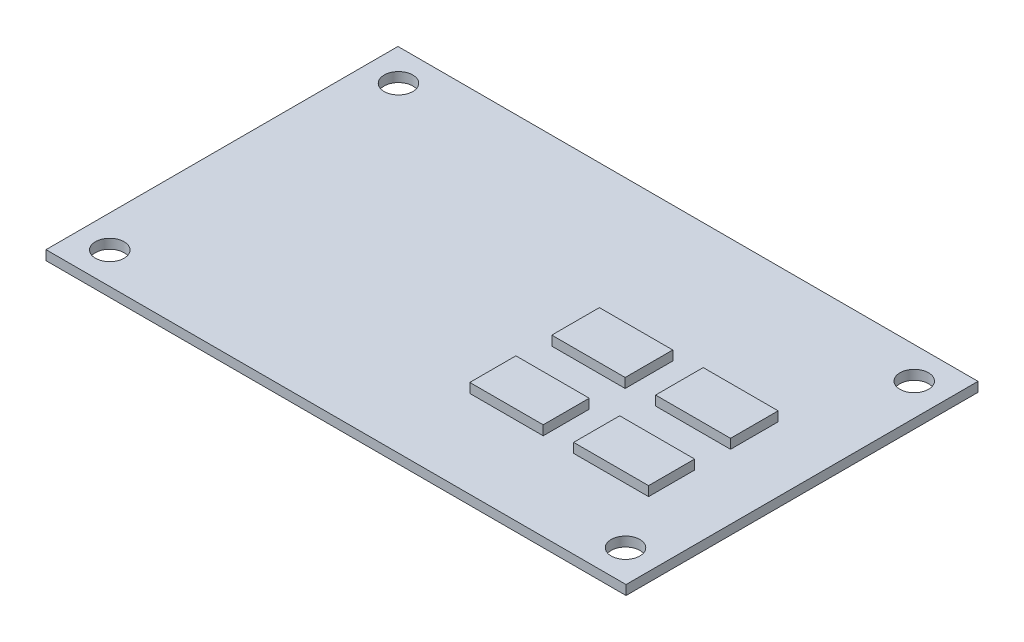
SolidWorks part; units mm, degrees
ref_plane "前视基准面" through (0, 0, 0) normal (0, 0, 1) x (1, 0, 0)
ref_plane "上视基准面" through (0, 0, 0) normal (0, 1, 0) x (1, 0, 0)
ref_plane "右视基准面" through (0, 0, 0) normal (1, 0, 0) x (0, 0, -1)
sketch "草图2" plane through (0, 0, 0) normal (0, 1, 0) x (1, 0, 0)
  line L1 (-30.365, 18.425) -> (30.365, 18.425)
  line L2 (-30.365, 18.425) -> (-30.365, -18.425)
  line L3 (-30.365, -18.425) -> (30.365, -18.425)
  line L4 (30.365, 18.425) -> (30.365, -18.425)
  line L5 (-30.365, 18.425) -> (30.365, -18.425) construction
  line L6 (-30.365, -18.425) -> (30.365, 18.425) construction
  point P0 (0, 0)
  dimension "D1" = 60.73
  dimension "D2" = 36.85
extrude "凸台-拉伸1" add sketch "草图2" along normal blind 1
hole_wizard "Ø3.0 (3) 直径孔1" positions "草图4" profile "草图5" hole size "Ø3.0" standard "GB"
sketch "草图4" plane through (0, 1, 0) normal (0, 1, 0) x (1, 0, 0)
  line L0 (36.5159, 0) -> (0, 0) construction
  line L1 (0, 0) -> (0, 30.9046) construction
  point P0 (-27, 15.115)
  point P2 (27, 15.115)
  point P4 (27, -15.115)
  point P6 (-27, -15.115)
  dimension "D1" = 30.23
  dimension "D2" = 54
sketch "草图5" plane through (-27, 1, -15.115) normal (1, 0, 0) x (0, 0, 1)
  line L0 (0, 0) -> (0, 13.3013)
  line L1 (0, 13.3013) -> (1.5, 12.4)
  line L2 (1.5, 12.4) -> (1.5, 0)
  line L5 (1.5, 0) -> (0, 0)
  line L10 (0, 13.3013) -> (-1.5, 12.4) construction
  line L11 (0, -6.35) -> (0, 107.95) construction
  dimension "孔直径" = 3
  dimension "孔深度" = 12.4
  dimension "导头角度" = 118
sketch "草图6" plane through (0, 1, 0) normal (0, 1, 0) x (1, 0, 0)
  line L1 (4.8613, 4.2886) -> (12.5431, 4.2886)
  line L2 (4.8613, 4.2886) -> (4.8613, -0.6964)
  line L3 (4.8613, -0.6964) -> (12.5431, -0.6964)
  line L4 (12.5431, 4.2886) -> (12.5431, -0.6964)
  line L5 (15.7303, 4.2886) -> (23.5755, 4.2886)
  line L6 (15.7303, 4.2886) -> (15.7303, -0.6964)
  line L7 (15.7303, -0.6964) -> (23.5755, -0.6964)
  line L8 (23.5755, 4.2886) -> (23.5755, -0.6964)
  line L9 (4.8613, -4.4556) -> (12.5431, -4.4556)
  line L10 (4.8613, -4.4556) -> (4.8613, -9.2772)
  line L11 (4.8613, -9.2772) -> (12.5431, -9.2772)
  line L12 (12.5431, -4.4556) -> (12.5431, -9.2772)
  line L13 (15.7303, -4.4556) -> (23.5755, -4.4556)
  line L14 (15.7303, -4.4556) -> (15.7303, -9.2772)
  line L15 (15.7303, -9.2772) -> (23.5755, -9.2772)
  line L16 (23.5755, -4.4556) -> (23.5755, -9.2772)
extrude "凸台-拉伸2" add sketch "草图6" along normal blind 1
